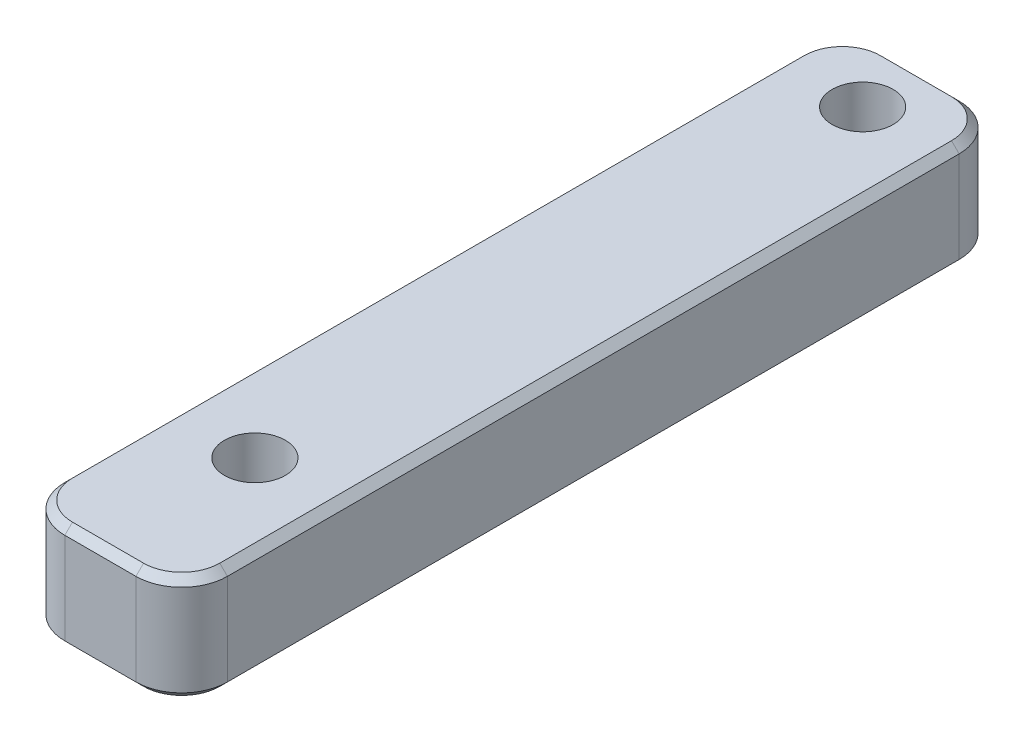
SolidWorks part; units mm, degrees
material "5052-O"
ref_plane "正面" through (0, 0, 0) normal (0, 0, 1) x (1, 0, 0)
ref_plane "平面" through (0, 0, 0) normal (0, 1, 0) x (1, 0, 0)
ref_plane "右側面" through (0, 0, 0) normal (1, 0, 0) x (0, 0, -1)
sketch "ｽｹｯﾁ1" plane through (0, 0, 0) normal (0, 1, 0) x (1, 0, 0)
  line L0 (0, 0) -> (5.3326, 0)
  line L1 (5.3326, 0) -> (5.3326, 27)
  line L2 (5.3326, 27) -> (0, 27)
  line L3 (0, 27) -> (0, 0)
  line L4 (-15.6122, -3.9144) -> (-15.6122, -3.5244)
extrude "ﾎﾞｽ - 押し出し1" add sketch "ｽｹｯﾁ1" along normal blind 3.5 contours L2 L3 L0 L1
fillet "ﾌｨﾚｯﾄ1" radius 1.5 4 edges at (5.3326, 1.75, 0) (0, 1.75, 0) (0, 1.75, -27) (5.3326, 1.75, -27)
sketch "ｽｹｯﾁ2" plane through (0, 3.5, 0) normal (0, 1, 0) x (1, 0, 0)
  circle A0 centre (2.6663, 25) radius 1
  circle A1 centre (2.6663, 5.0674) radius 1
extrude "ｶｯﾄ - 押し出し1" cut sketch "ｽｹｯﾁ2" against normal through all
chamfer "面取り1" distance 0.25 angle 45 16 edges at (4.8932, 3.5, -0.4393) (2.6663, 3.5, 0) (0.4393, 3.5, -0.4393) (0, 3.5, -13.5) (0.4393, 3.5, -26.5607) (5.3326, 3.5, -13.5) (4.8932, 3.5, -26.5607) (2.6663, 3.5, -27) (0.4393, 0, -0.4393) (2.6663, 0, 0) (4.8932, 0, -0.4393) (5.3326, 0, -13.5) (0, 0, -13.5) (0.4393, 0, -26.5607) (2.6663, 0, -27) (4.8932, 0, -26.5607)
